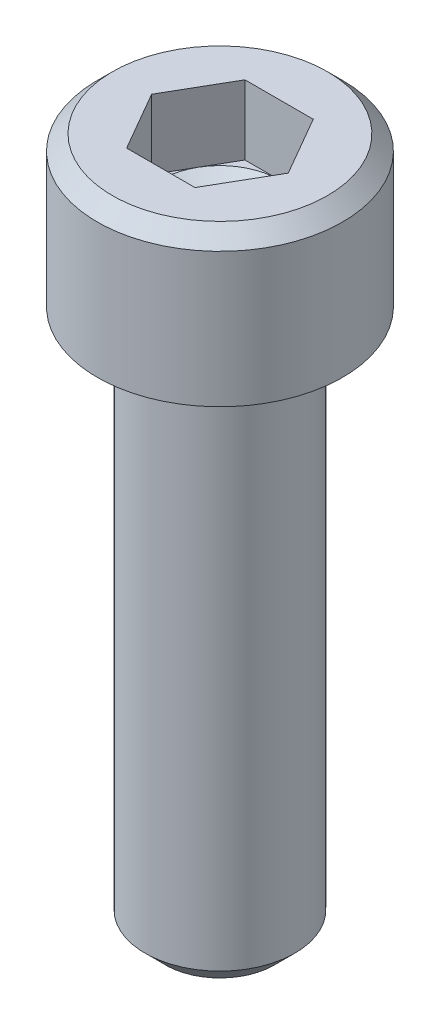
SolidWorks part; units mm, degrees
material "Alloy Steel"
ref_plane "Front Plane" through (0, 0, 0) normal (0, 0, 1) x (1, 0, 0)
ref_plane "Top Plane" through (0, 0, 0) normal (0, 1, 0) x (1, 0, 0)
ref_plane "Right Plane" through (0, 0, 0) normal (1, 0, 0) x (0, 0, -1)
sketch "Sketch5" plane through (0, 0, 0) normal (0, 0, 1) x (1, 0, 0)
  line L0 (0, 1.0804) -> (0, -12.7)
  line L2 (0, 3.5052) -> (0, 5.8988) construction
  line L3 (2.5146, 3.5052) -> (1.3843, 3.5052)
  line L6 (2.8702, 3.1496) -> (2.5146, 3.5052)
  line L7 (1.3843, 1.8796) -> (1.3843, 3.5052)
  line L8 (0, 1.0804) -> (1.3843, 1.8796)
  line L10 (2.8702, 0) -> (2.8702, 3.1496)
  line L14 (2.0066, 0) -> (2.8702, 0)
  line L19 (1.7526, -0.254) -> (1.7526, -12.2276)
  line L23 (1.2802, -12.7) -> (1.7526, -12.2276)
  line L25 (0, -12.7) -> (1.2802, -12.7)
  arc A2 (2.0066, 0) -> (1.7526, -0.254) centre (2.0066, -0.254) ccw
revolve "Revolve2" add sketch "Sketch5" angle 360 about L2
sketch "Sketch3" plane through (0, 3.5052, 0) normal (0, 1, 0) x (1, 0, 0)
  line L0 (-1.5985, 0) -> (-0.7992, -1.3843)
  line L1 (-0.7992, -1.3843) -> (0.7992, -1.3843)
  line L2 (0.7992, -1.3843) -> (1.5985, 0)
  line L3 (1.5985, 0) -> (0.7992, 1.3843)
  line L4 (0.7992, 1.3843) -> (-0.7992, 1.3843)
  line L5 (-0.7992, 1.3843) -> (-1.5985, 0)
extrude "Cut-Extrude1" cut sketch "Sketch3" against normal blind 1.6256
